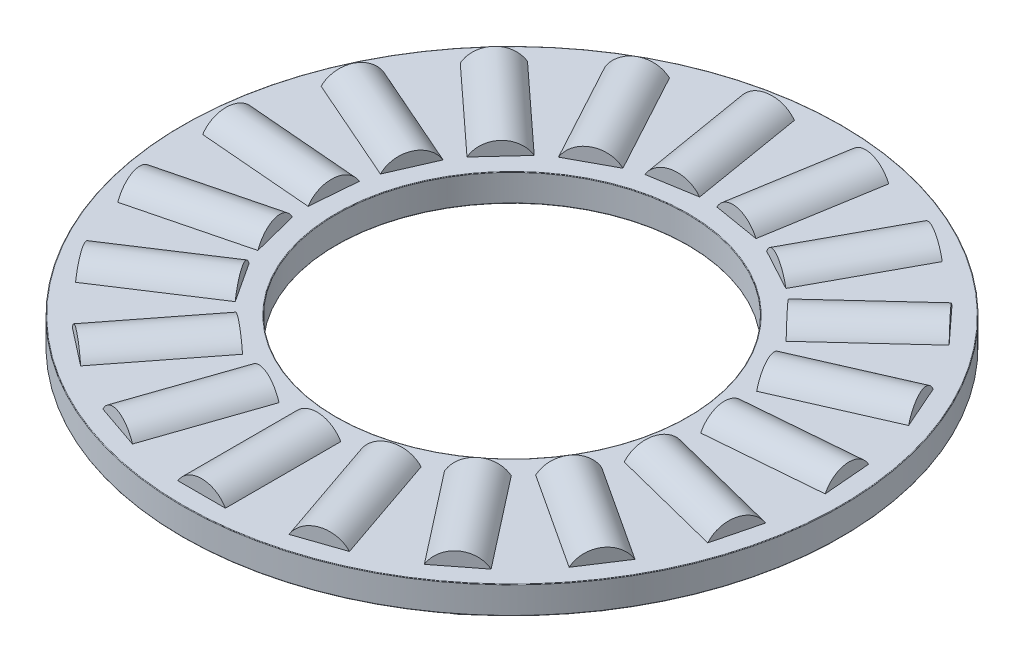
SolidWorks part; units mm, degrees
ref_plane "Front Plane" through (0, 0, 0) normal (0, 0, 1) x (1, 0, 0)
ref_plane "Top Plane" through (0, 0, 0) normal (0, 1, 0) x (1, 0, 0)
ref_plane "Right Plane" through (0, 0, 0) normal (1, 0, 0) x (0, 0, -1)
sketch "Sketch1" plane through (0, 0, 0) normal (1, 0, 0) x (0, 0, -1)
  line L0 (-11.9062, 0) -> (11.9062, 0) construction
  line L1 (0, -0.9922) -> (0, 0.9922) construction
  line L2 (-11.9063, 0.4961) -> (-6.35, 0.4961)
  line L3 (-11.9063, 0.4961) -> (-11.9063, -0.4961)
  line L4 (-11.9063, -0.4961) -> (-6.35, -0.4961)
  line L5 (-6.35, 0.4961) -> (-6.35, -0.4961)
  line L7 (-9.1281, 0.9922) -> (-9.1281, 0.4961) construction
  line L8 (-11.2117, 0.9922) -> (-7.0445, 0.9922) construction
  line L9 (-11.2117, 0.9922) -> (-11.2117, -0.9922) construction
  line L10 (-11.2117, -0.9922) -> (-7.0445, -0.9922) construction
  line L11 (-7.0445, 0.9922) -> (-7.0445, -0.9922) construction
  point P16 (-11.2117, 0)
  dimension "OD" = 23.8125
  dimension "Shaft Dia" = 12.7
  dimension "Th" = 1.9844
  dimension "D2" = 0.9922
  dimension "D1" = 4.1672
  dimension "D3" = 5.5562
revolve "Revolve1" add sketch "Sketch1" angle 360 about L1
sketch "Sketch3" plane through (0, 0, 0) normal (1, 0, 0) x (0, 0, -1)
  line L0 (-11.2117, 0.9922) -> (-11.2117, -0.9922) construction
  line L1 (-11.2117, 0) -> (-7.0445, 0)
  line L2 (-11.2117, 0) -> (-11.2117, 0.9922)
  line L3 (-11.2117, 0.9922) -> (-7.0445, 0.9922)
  line L4 (-7.0445, 0) -> (-7.0445, 0.9922)
revolve "Cut-Revolve1" cut sketch "Sketch3" angle 360 about L1
sketch "Sketch2" plane through (0, 0, 0) normal (1, 0, 0) x (0, 0, -1)
  line L1 (-11.2117, 0) -> (-7.0445, 0)
  line L2 (-11.2117, 0) -> (-11.2117, 0.9922)
  line L3 (-11.2117, 0.9922) -> (-7.0445, 0.9922)
  line L4 (-7.0445, 0) -> (-7.0445, 0.9922)
revolve "Revolve2" add sketch "Sketch2" angle 360 about L1
ref_axis "Axis1" through (0, 0.9922, 0) along (0, -1, 0)
pattern_circular "CirPattern1" count 19 every 18.947 about axis through (0, 0.9922, 0) along (0, -1, 0) of bodies 187 411
pattern_circular "CirPattern2" count 19 every 18.947 about axis through (0, 0, 0) along (0, 1, 0) of "Cut-Revolve1"
sketch "Sketch4" plane through (0, 0, 0) normal (1, 0, 0) x (0, 0, -1)
  line L0 (-11.9063, 0.4961) -> (-11.9063, -0.4961) construction
  line L1 (-11.9062, 9.1091) -> (-6.35, 9.1091)
  line L2 (-11.9062, 9.1091) -> (-11.9062, 9.9219)
  line L3 (-11.9062, 9.9219) -> (-6.35, 9.9219)
  line L4 (-6.35, 9.1091) -> (-6.35, 9.9219)
  line L5 (-11.9062, -9.9219) -> (-6.35, -9.9219)
  line L6 (-11.9062, -9.9219) -> (-11.9062, -9.1091)
  line L7 (-11.9062, -9.1091) -> (-6.35, -9.1091)
  line L8 (-6.35, -9.9219) -> (-6.35, -9.1091)
  line L10 (-6.35, 0.4961) -> (-6.35, -0.4961) construction
  line L11 (0, 0) -> (-11.9062, 0) construction
  line L12 (-11.9062, 0) -> (11.9062, 0) construction
  line L13 (0, -0.9922) -> (0, 0.9922) construction
  dimension "Ht" = 19.8438
  dimension "Washer Th" = 0.8128
  dimension "Washer ID" = 12.7
  dimension "Washer OD" = 23.8125
revolve "Revolve3" [suppressed] add sketch "Sketch4" angle 360 about L1
fillet "Fillet1" [suppressed] radius 0.0198
fillet "Fillet2" radius 0.0198 4 edges at (0, -0.4961, -6.35) (0, 0.4961, -6.35) (0, -0.4961, -11.9063) (0, 0.4961, -11.9063)
fillet "Fillet3" [suppressed] radius 0.0198
equation "\"D2@Sketch1\" = \"Th@Sketch1\"*.5"
equation "\"D1@Fillet1\" = \"Th@Sketch1\"*.01"
equation "\"D1@Fillet2\" = \"D1@Fillet1\""
equation "\"D1@Fillet3\" = \"D1@Fillet1\""
equation "\"D1@Sketch1\" = \"D3@Sketch1\"*.75"
equation "\"Angle@CirPattern1\" = 360/\"Rollers@CirPattern1\""
equation "\"Rollers@CirPattern1\" = \"OD@Sketch1\"*20"
equation "\"D1@CirPattern2\" = \"Rollers@CirPattern1\""
equation "\"D2@CirPattern2\" = \"Angle@CirPattern1\""
equation "\"Ht@Sketch4\" = \"Th@Sketch1\"*10"
